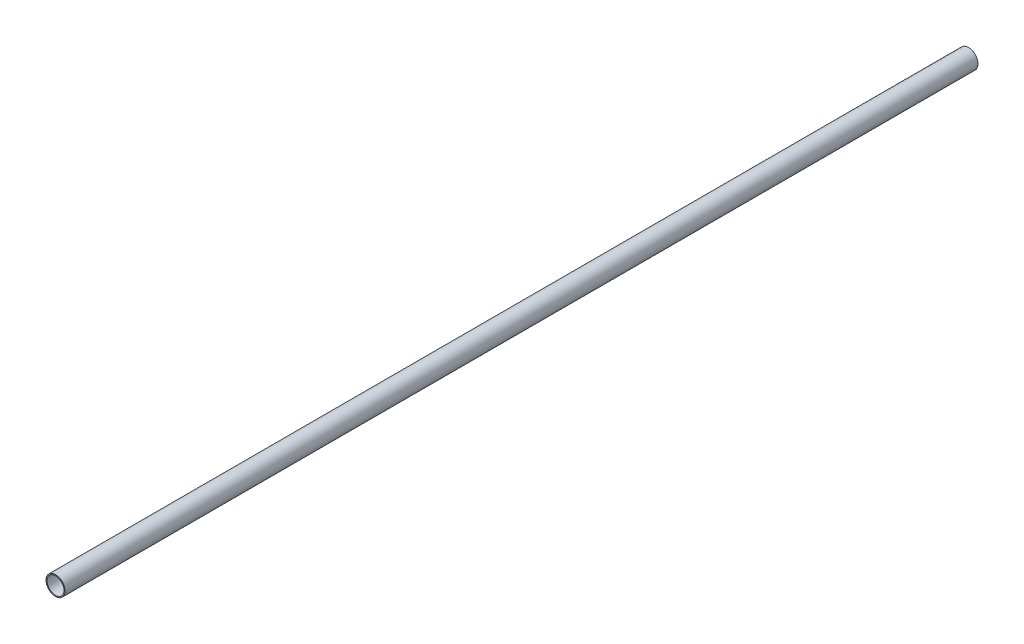
SolidWorks part; units mm, degrees
ref_plane "Front" through (0, 0, 0) normal (0, 0, 1) x (1, 0, 0)
ref_plane "Top" through (0, 0, 0) normal (0, 1, 0) x (1, 0, 0)
ref_plane "Side" through (0, 0, 0) normal (1, 0, 0) x (0, 0, -1)
sketch "PipeSketch" plane through (0, 0, 0) normal (0, 0, 1) x (1, 0, 0)
  circle A0 centre (0, 0) radius 57.15
  circle A1 centre (0, 0) radius 51.1302
  dimension "OuterDiameter" = 114.3
  dimension "InnerDiameter" = 102.2604
extrude "Extrusion" add sketch "PipeSketch" along normal blind 5486.4
sketch "FilterSketch" plane through (0, 0, 0) normal (0, 0, 1) x (1, 0, 0)
  circle A0 centre (0, 0) radius 50.8 construction
  dimension "NominalDiameter" = 101.6
